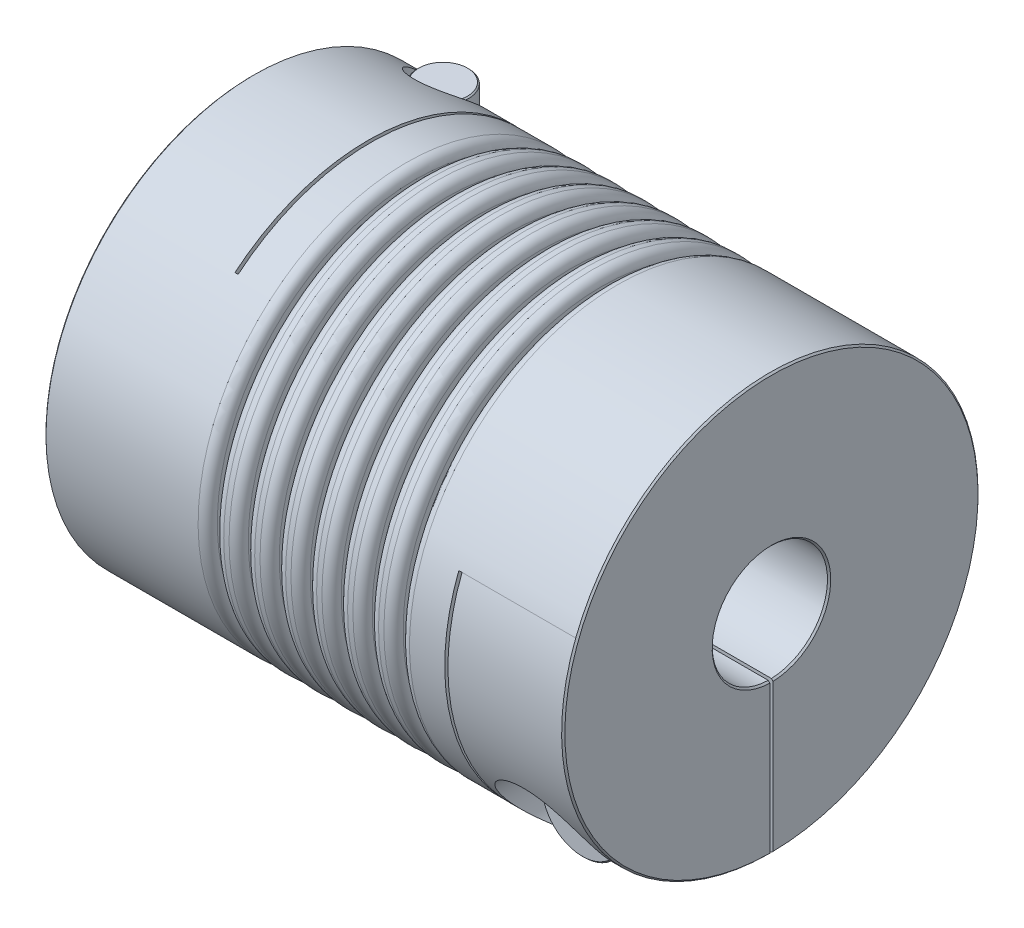
SolidWorks part; units mm, degrees
ref_plane "Front Plane" through (0, 0, 0) normal (0, 0, 1) x (1, 0, 0)
ref_plane "Top Plane" through (0, 0, 0) normal (0, 1, 0) x (1, 0, 0)
ref_plane "Right Plane" through (0, 0, 0) normal (1, 0, 0) x (0, 0, -1)
sketch "Sketch1" plane through (0, 0, 0) normal (1, 0, 0) x (0, 0, -1)
  circle A0 centre (0, 0) radius 32.5
  dimension "dim D" = 65
extrude "Boss-Extrude1" add sketch "Sketch1" along normal mid plane 81
sketch "Sketch2" plane through (40.5, 0, 0) normal (1, 0, 0) x (0, 0, -1)
  circle A0 centre (0, 0) radius 9
  dimension "dim D1" = 18
extrude "Cut-Extrude1" cut sketch "Sketch2" against normal through all
chamfer "Chamfer1" distance 0.254 angle 45 4 edges at (-40.5, 0, -9) (-40.5, 0, -32.5) (40.5, 0, -32.5) (40.5, 0, -9)
ref_plane "Plane2" through (0, -32.5, 0) normal (0, -1, 0) x (1, 0, 0)
ref_plane "F" through (-31.5, 0, 0) normal (-1, 0, 0) x (0, 0, 1)
sketch "Sketch4" plane through (0, -32.5, 0) normal (0, -1, 0) x (1, 0, 0)
  line L0 (-40.246, -32.5) -> (40.246, -32.5) construction
  line L1 (-22.5, -32.5) -> (-22, -32.5)
  line L2 (-22.5, -32.5) -> (-22.5, 20.75)
  line L3 (-22.5, 20.75) -> (-22, 20.75)
  line L4 (-22, -32.5) -> (-22, 20.75)
  line L5 (-22.5, 9) -> (-22.5, 32.5) construction
  line L6 (40.246, 9) -> (-40.246, 9) construction
  line L7 (40.246, 32.5) -> (-40.246, 32.5) construction
  line L10 (-22.5, 20.75) -> (-40.5, 20.75) construction
  line L11 (-40.5, 32.246) -> (-40.5, -32.246) construction
  line L12 (-31.5, 10.2256) -> (-31.5, -10.2256) construction
  point P16 (-31.5, 20.75)
  dimension "D1" = 0.5
extrude "Cut-Extrude2" cut sketch "Sketch4" against normal through all
ref_plane "Plane4" through (0, 0, -32.5) normal (0, 0, -1) x (-1, 0, 0)
sketch "Sketch7" plane through (0, 0, -32.5) normal (0, 0, -1) x (-1, 0, 0)
  line L1 (-22, -32.5) -> (-22.5, -32.5)
  line L2 (-22.5, -32.5) -> (-22.5, 11.75)
  line L3 (-22.5, 11.75) -> (-22, 11.75)
  line L4 (-22, -32.5) -> (-22, 11.75)
  line L5 (40.5, 8.6487) -> (31.5, 8.6487) construction
  line L7 (-10.505, -32.5) -> (10.505, -32.5) construction
  line L8 (-40.246, -9) -> (22, -9) construction
  line L9 (40.5, -32.246) -> (40.5, 32.246) construction
  line L10 (-40.246, -9) -> (22, -9) construction
  line L11 (22, 25.0137) -> (22.5, 25.0137) construction
  line L12 (-22.5, 11.75) -> (-22.5, -32.5) construction
  line L14 (-40.246, -9) -> (22, -9) construction
  line L16 (-40.246, -9) -> (22, -9) construction
  line L17 (22.5, -32.5) -> (40.246, -32.5) construction
  line L18 (31.5, -10.2256) -> (31.5, 10.2256) construction
  line L19 (-40.246, -32.5) -> (-40.246, 32.5) construction
  line L20 (-40.5, 11.75) -> (-31.5, 11.75) construction
  line L21 (-40.5, 32.246) -> (-40.5, -32.246) construction
  line L22 (-31.5, 11.75) -> (-22.5, 11.75) construction
  line L23 (-40.246, -32.5) -> (-40.246, 32.5) construction
  line L24 (-40.246, -9) -> (-40.246, 32.5) construction
  line L25 (-40.246, -9) -> (22, -9) construction
  point P23 (-22.5, 11.75)
  point P33 (-40.246, 11.75)
extrude "Cut-Extrude3" cut sketch "Sketch7" against normal through all
sketch "Sketch8" plane through (0, 0, 0) normal (0, 1, 0) x (1, 0, 0)
  line L0 (-22.5, -20.75) -> (-22.5, 32.5) construction
  line L1 (-40.5, 32.5) -> (-22.5, 32.5)
  line L2 (-40.5, 32.5) -> (-40.5, 0)
  line L3 (-40.5, 0) -> (-22.5, 0)
  line L4 (-22.5, 32.5) -> (-22.5, 0)
  line L5 (10.505, 32.5) -> (-10.505, 32.5) construction
  line L6 (-40.5, 32.246) -> (-40.5, -32.246) construction
extrude "Cut-Extrude5" cut sketch "Sketch8" against normal mid plane 0.5
sketch "Sketch13" plane through (0, 0, 0) normal (0, 0, 1) x (1, 0, 0)
  line L0 (40.5, -32.246) -> (40.5, 32.246) construction
  line L1 (22.5, -32.5) -> (40.5, -32.5)
  line L2 (22.5, -32.5) -> (22.5, 0)
  line L3 (22.5, 0) -> (40.5, 0)
  line L4 (40.5, -32.5) -> (40.5, 0)
extrude "Cut-Extrude6" cut sketch "Sketch13" against normal mid plane 0.5
hole_wizard "CBORE for M8 SHCS2" positions "Sketch12" profile "Sketch11" counterbore size "M8" standard "Ansi Metric" end condition through all
sketch "Sketch12" plane through (0, -32.5, 0) normal (0, -1, 0) x (1, 0, 0)
  line L0 (-31.5, 10.2256) -> (-31.5, -10.2256) construction
  line L1 (-22.5, -8.9965) -> (-22.5, -32.499) construction
  line L2 (-22.5, -8.9965) -> (-22.5, -32.499)
  line L3 (-22.5, -20.7478) -> (-31.5, -20.7478) construction
  point P0 (-31.5, -20.7478)
sketch "Sketch11" plane through (-31.5, -32.5, -20.7478) normal (1, 0, 0) x (0, 0, -1)
  line L0 (0, 0) -> (0, 65)
  line L1 (0, 65) -> (4.5, 65)
  line L3 (4.5, 65) -> (4.5, 20)
  line L4 (4.5, 20) -> (7.5, 20)
  line L5 (7.5, 20) -> (7.5, 0)
  line L7 (7.5, 0) -> (0, 0)
  line L11 (0, -6.35) -> (0, 107.95) construction
  dimension "Thru Hole Dia." = 9
  dimension "Thru Hole Depth" = 65
  dimension "C'Bore Dia." = 15
  dimension "C'Bore Depth" = 20
ref_plane "Plane5" through (0, 0, 32.5) normal (0, 0, 1) x (1, 0, 0)
hole_wizard "CBORE for M8 SHCS1" positions "Sketch15" profile "Sketch14" counterbore size "M8" standard "Ansi Metric" end condition through all
sketch "Sketch15" plane through (0, 0, 32.5) normal (0, 0, 1) x (1, 0, 0)
  line L0 (-39, -12.5) -> (-24, -12.5) construction
  line L1 (-39, -12.5) -> (-24, -12.5)
  line L5 (0, 0) -> (0, 32.5) construction
  line L6 (-22.5, 32.5) -> (-40.246, 32.5) construction
  line L8 (39, -12.5) -> (24, -12.5)
  line L9 (31.5, -12.5) -> (31.5, -20.7478) construction
  line L11 (31.5, -32.499) -> (31.5, -8.9965) construction
  line L12 (40.246, -32.499) -> (22.5, -32.499) construction
  line L13 (22.5, -8.9965) -> (40.246, -8.9965) construction
  point P0 (31.5, -20.7478)
sketch "Sketch14" plane through (31.5, -20.7478, 32.5) normal (1, 0, 0) x (0, -1, 0)
  line L0 (0, 0) -> (0, 65)
  line L1 (0, 65) -> (4.5, 65)
  line L3 (4.5, 65) -> (4.5, 20)
  line L4 (4.5, 20) -> (7.5, 20)
  line L5 (7.5, 20) -> (7.5, 0)
  line L7 (7.5, 0) -> (0, 0)
  line L11 (0, -6.35) -> (0, 107.95) construction
  dimension "Thru Hole Dia." = 9
  dimension "Thru Hole Depth" = 65
  dimension "C'Bore Dia." = 15
  dimension "C'Bore Depth" = 20
sketch "Sketch16" plane through (0, 0, 12.5) normal (0, 0, 1) x (1, 0, 0)
  circle A0 centre (31.5, -20.7478) radius 6.5
  dimension "screw dia" = 13
extrude "Boss-Extrude2" add sketch "Sketch16" along normal blind 8 separate body
sketch "Sketch17" plane through (0, 0, 12.5) normal (0, 0, -1) x (-1, 0, 0)
  circle A0 centre (-31.5, -20.7478) radius 4
  dimension "D1" = 8
extrude "Boss-Extrude3" add sketch "Sketch17" along normal blind 38
chamfer "Chamfer2" distance 0.2 angle 45 3 edges at (27.5, -20.7478, -25.5) (38, -20.7478, 12.5) (38, -20.7478, 20.5)
sketch "Sketch18" plane through (0, 0, 20.5) normal (0, 0, 1) x (1, 0, 0)
  line L1 (31.5, -24.2119) -> (34.5, -22.4798)
  line L2 (34.5, -22.4798) -> (34.5, -19.0157)
  line L3 (34.5, -19.0157) -> (31.5, -17.2837)
  line L4 (31.5, -17.2837) -> (28.5, -19.0157)
  line L5 (28.5, -19.0157) -> (28.5, -22.4798)
  line L6 (28.5, -22.4798) -> (31.5, -24.2119)
  circle A0 centre (31.5, -20.7478) radius 3 construction
  dimension "hex" = 6
extrude "Cut-Extrude7" cut sketch "Sketch18" against normal blind 1.5
mirror "Mirror1" about plane through (0, 0, 0) normal (1, 0, 0) of bodies 121
pattern_circular "CirPattern1" count 2 every 90 about axis through (0, 0, 0) along (1, 0, 0) of bodies 122 117
delete or keep bodies "Body-Delete1" type delete bodies bodies 122
sketch "Sketch19" plane through (0, 0, 0) normal (0, 0, 1) x (1, 0, 0)
  line L0 (-40.5, -22.5) -> (40.5, -22.5) construction
  line L1 (-40.5, 32.246) -> (-40.5, -32.246) construction
  line L2 (40.5, -32.245) -> (40.5, 32.246) construction
  line L3 (0, 0) -> (0, -22.5) construction
  line L4 (0, 0) -> (0, 22.5) construction
  line L5 (40.246, 32.5) -> (-22, 32.5) construction
  line L6 (-0.5, 32.5) -> (0.5, 32.5)
  line L7 (-0.5, 32.5) -> (-0.5, 22.5)
  line L8 (-0.5, 22.5) -> (0.5, 22.5)
  line L9 (0.5, 32.5) -> (0.5, 22.5)
  line L10 (4.3333, 32.5) -> (5.3333, 32.5)
  line L11 (4.3333, 32.5) -> (4.3333, 22.5)
  line L12 (4.3333, 22.5) -> (5.3333, 22.5)
  line L13 (5.3333, 32.5) -> (5.3333, 22.5)
  line L14 (9.1667, 32.5) -> (10.1667, 32.5)
  line L15 (9.1667, 32.5) -> (9.1667, 22.5)
  line L16 (9.1667, 22.5) -> (10.1667, 22.5)
  line L17 (10.1667, 32.5) -> (10.1667, 22.5)
  line L18 (14, 32.5) -> (15, 32.5)
  line L19 (14, 32.5) -> (14, 22.5)
  line L20 (14, 22.5) -> (15, 22.5)
  line L21 (15, 32.5) -> (15, 22.5)
  line L22 (-15, 32.5) -> (-15, 22.5)
  line L23 (-14, 22.5) -> (-15, 22.5)
  line L24 (-14, 32.5) -> (-14, 22.5)
  line L25 (-14, 32.5) -> (-15, 32.5)
  line L26 (-10.1667, 32.5) -> (-10.1667, 22.5)
  line L27 (-9.1667, 22.5) -> (-10.1667, 22.5)
  line L28 (-9.1667, 32.5) -> (-9.1667, 22.5)
  line L29 (-9.1667, 32.5) -> (-10.1667, 32.5)
  line L30 (-5.3333, 32.5) -> (-5.3333, 22.5)
  line L31 (-4.3333, 22.5) -> (-5.3333, 22.5)
  line L32 (-4.3333, 32.5) -> (-4.3333, 22.5)
  line L33 (-4.3333, 32.5) -> (-5.3333, 32.5)
  line L34 (0, 0) -> (-40.5, 0) construction
  dimension "D1" = 1
  dimension "Dim E" = 45
  dimension "Dim L1" = 25.5
  dimension "D2" = 4
revolve "Cut-Revolve1" cut sketch "Sketch19" angle 360 about L34
fillet "Fillet1" radius 1.5 14 edges at (-14, 32.5, 0) (-10.1667, 32.5, 0) (-9.1667, 32.5, 0) (-5.3333, 32.5, 0) (-0.5, 32.5, 0) (-4.3333, 32.5, 0) (0.5, 32.5, 0) (4.3333, 32.5, 0) (5.3333, 32.5, 0) (9.1667, 32.5, 0) (10.1667, 32.5, 0) (14, 32.5, 0) (15, 32.5, 0) (-15, 32.5, 0)
fillet "Fillet2" radius 0.1 14 edges at (14, 22.5, 0) (15, 22.5, 0) (9.1667, 22.5, 0) (10.1667, 22.5, 0) (4.3333, 22.5, 0) (5.3333, 22.5, 0) (-0.5, 22.5, 0) (0.5, 22.5, 0) (-5.3333, 22.5, 0) (-4.3333, 22.5, 0) (-10.1667, 22.5, 0) (-9.1667, 22.5, 0) (-15, 22.5, 0) (-14, 22.5, 0)
